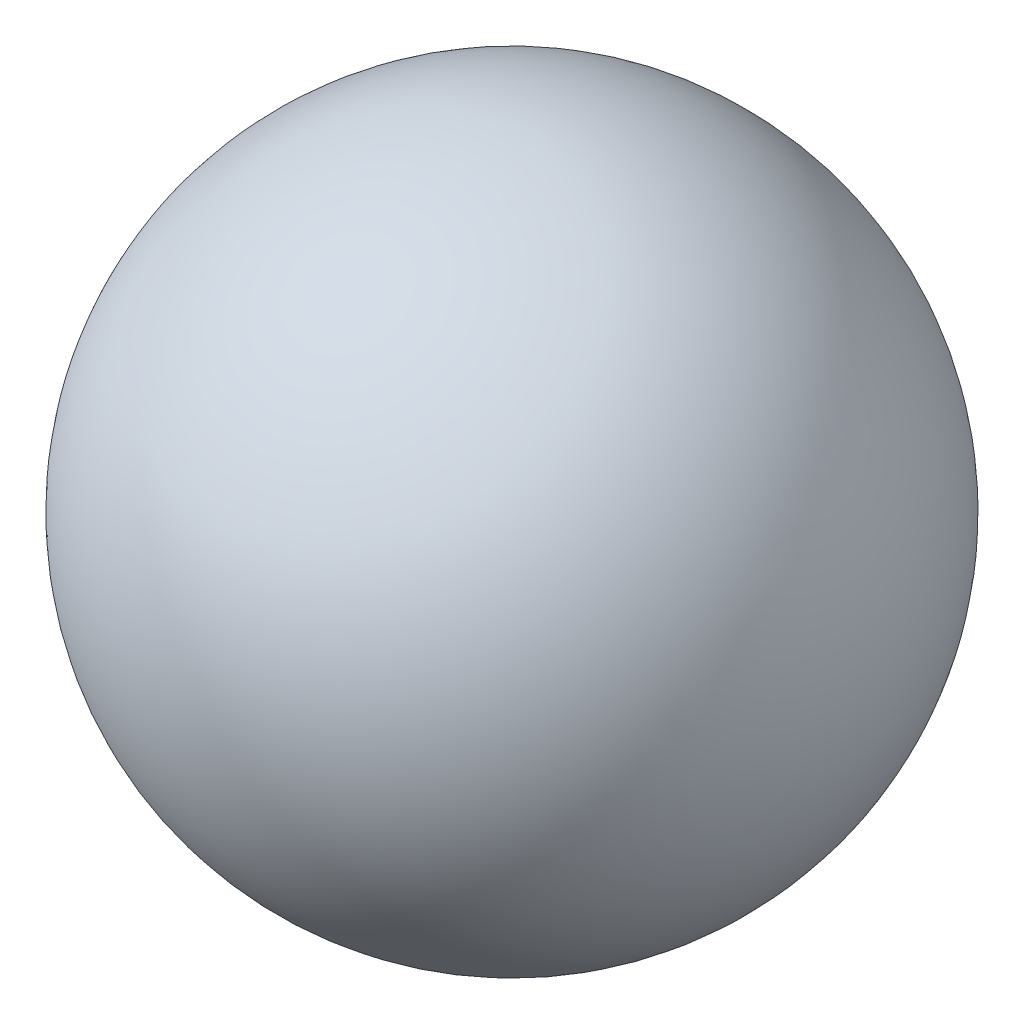
SolidWorks part; units mm, degrees
ref_plane "Front Plane" through (0, 0, 0) normal (0, 0, 1) x (1, 0, 0)
ref_plane "Top Plane" through (0, 0, 0) normal (0, 1, 0) x (1, 0, 0)
ref_plane "Right Plane" through (0, 0, 0) normal (1, 0, 0) x (0, 0, -1)
sketch "Sketch1" plane through (0, 0, 0) normal (0, 0, 1) x (1, 0, 0)
  line L0 (-12, 0) -> (12, 0)
  arc A0 (-12, 0) -> (12, 0) centre (0, 0) ccw
  point P4 (0, 0)
  dimension "D1" = 24
revolve "Revolve1" add sketch "Sketch1" angle 360 about L0
